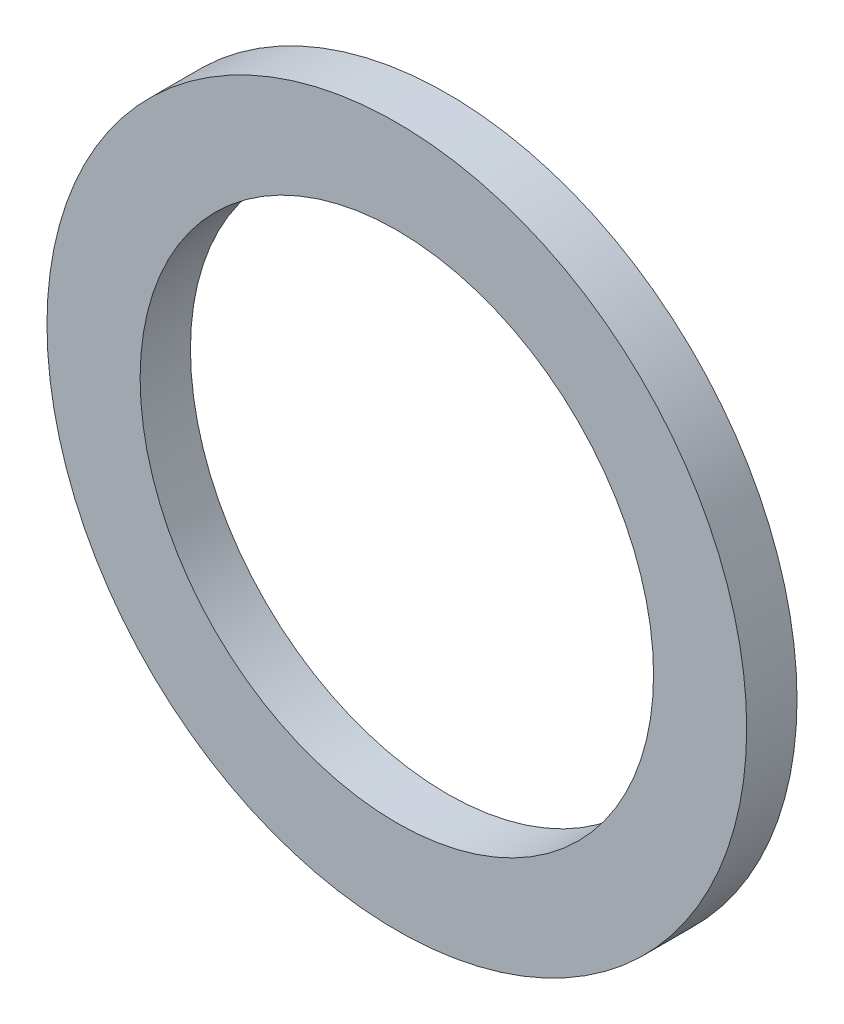
SolidWorks part; units mm, degrees
ref_plane "Front Plane" through (0, 0, 0) normal (0, 0, 1) x (1, 0, 0)
ref_plane "Top Plane" through (0, 0, 0) normal (0, 1, 0) x (1, 0, 0)
ref_plane "Right Plane" through (0, 0, 0) normal (1, 0, 0) x (0, 0, -1)
sketch "Sketch1" plane through (0, 0, 0) normal (0, 0, 1) x (1, 0, 0)
  circle A0 centre (0, 0) radius 5.1
  circle A1 centre (0, 0) radius 6.95
  dimension "ID" = 10.2
  dimension "OD" = 13.9
sketch "Sketch2" plane through (0, 0, 0) normal (1, 0, 0) x (0, 0, -1)
  line L0 (0.5, 0) -> (-0.5, 0)
  point P4 (0, 0)
  dimension "Thickness Avg" = 1
sketch "Sketch3" plane through (0, 0, 0) normal (0, 0, 1) x (1, 0, 0)
  circle A0 centre (0, 0) radius 6.95 construction
  circle A1 centre (0, 0) radius 6.95
  circle A2 centre (0, 0) radius 5.1 construction
  circle A3 centre (0, 0) radius 5.1
extrude "Boss-Extrude1" add sketch "Sketch3" along normal mid plane 1
equation "\"D1@Boss-Extrude1\"=\"Thickness Avg@Sketch2\""
